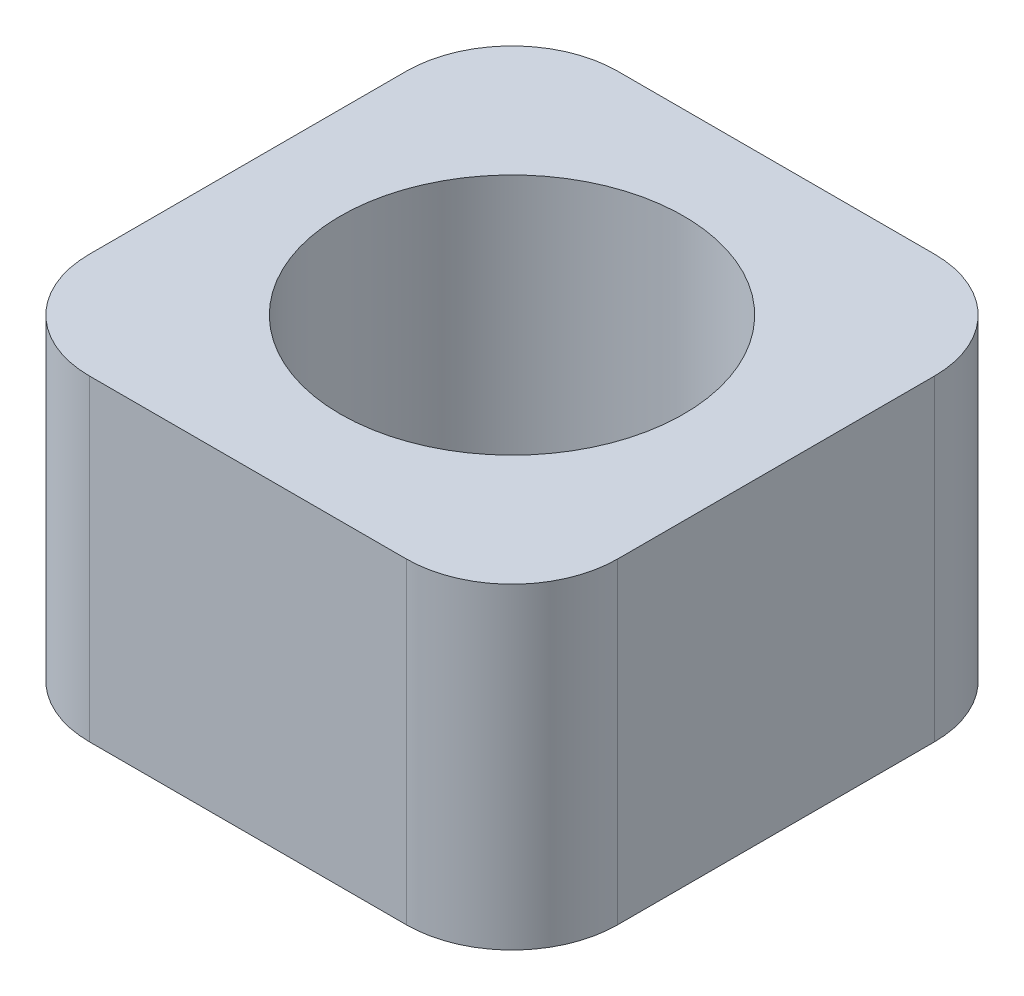
SolidWorks part; units mm, degrees
material "PET"
ref_plane "Front Plane" through (0, 0, 0) normal (0, 0, 1) x (1, 0, 0)
ref_plane "Top Plane" through (0, 0, 0) normal (0, 1, 0) x (1, 0, 0)
ref_plane "Right Plane" through (0, 0, 0) normal (1, 0, 0) x (0, 0, -1)
sketch "Sketch1" plane through (0, 0, 0) normal (0, 1, 0) x (1, 0, 0)
  line L1 (-5, -5) -> (5, -5)
  line L2 (-5, -5) -> (-5, 5)
  line L3 (-5, 5) -> (5, 5)
  line L4 (5, -5) -> (5, 5)
  line L5 (-5, -5) -> (5, 5) construction
  line L6 (-5, 5) -> (5, -5) construction
  circle A0 centre (0, 0) radius 5
  circle A1 centre (0, 0) radius 3.25
  dimension "D1" = 6.5
  dimension "D2" = 10
extrude "Boss-Extrude1" add sketch "Sketch1" along normal mid plane 6 contours A0 L3 L2 | A0 A1 | A0 L4 L3 | A0 L1 L4 | A0 L2 L1
fillet "Fillet1" radius 2 4 edges at (5, 0, -5) (5, 0, 5) (-5, 0, 5) (-5, 0, -5)
